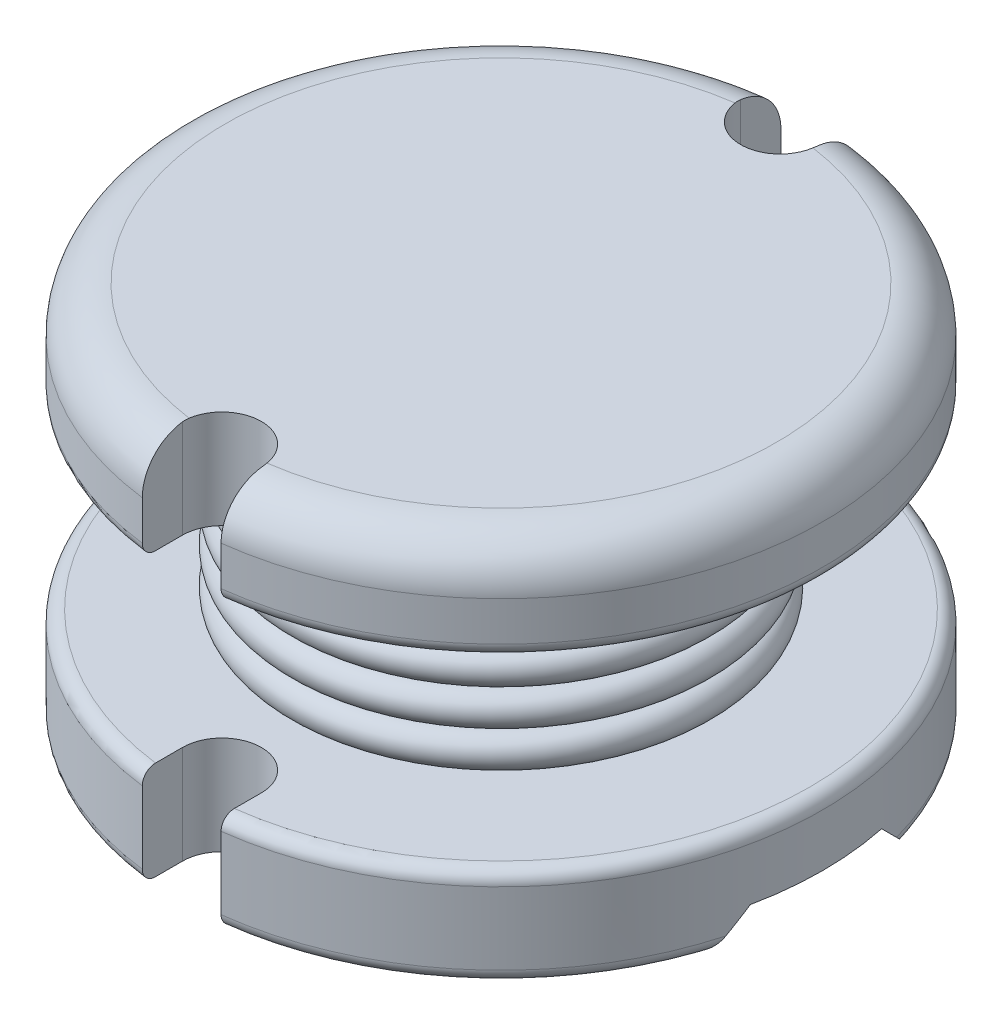
SolidWorks part; units mm, degrees
ref_plane "Front Plane" through (0, 0, 0) normal (0, 0, 1) x (1, 0, 0)
ref_plane "Top Plane" through (0, 0, 0) normal (0, 1, 0) x (1, 0, 0)
ref_plane "Right Plane" through (0, 0, 0) normal (1, 0, 0) x (0, 0, -1)
sketch "Sketch1" plane through (0, 0, 0) normal (0, 0, 1) x (1, 0, 0)
  line L0 (0, 0) -> (-4.7, 0)
  line L1 (-4.9, 0.2) -> (-4.9, 1.3)
  line L2 (-4.7, 1.5) -> (-2.6, 1.5)
  line L3 (-2.6, 1.5) -> (-2.6, 4.3)
  line L4 (-2.6, 4.3) -> (-4.7, 4.3)
  line L5 (-4.9, 4.5) -> (-4.9, 5.1)
  line L6 (-4.2, 5.8) -> (0, 5.8)
  line L7 (0, 5.8) -> (0, 0)
  arc A0 (-4.9, 5.1) -> (-4.2, 5.8) centre (-4.2, 5.1) cw
  arc A1 (-4.7, 0) -> (-4.9, 0.2) centre (-4.7, 0.2) cw
  arc A2 (-4.9, 1.3) -> (-4.7, 1.5) centre (-4.7, 1.3) cw
  arc A3 (-4.9, 4.5) -> (-4.7, 4.3) centre (-4.7, 4.5) ccw
  point P11 (-4.9, 5.8)
  point P14 (-4.9, 0)
  point P17 (-4.9, 1.5)
  point P20 (-4.9, 4.3)
  dimension "D6" = 0.7
  dimension "D7" = 0.2
  dimension "D1" = 5.8
  dimension "D2" = 4.9
  dimension "D3" = 1.5
  dimension "D4" = 1.5
  dimension "D5" = 2.6
revolve "Revolve1" add sketch "Sketch1" angle 360 about L7
sketch "Sketch2" plane through (0, 5.8, 0) normal (0, 1, 0) x (1, 0, 0)
  line L0 (0, 0) -> (0, 6) construction
  line L1 (0, 0) -> (0, -6) construction
  line L2 (-0.6, 6) -> (0.6, 6)
  line L3 (0.6, 6) -> (0.6, 4.25)
  line L4 (-0.6, 6) -> (-0.6, 4.25)
  line L5 (-0.6, -6) -> (0.6, -6)
  line L6 (0.6, -6) -> (0.6, -4.25)
  line L7 (-0.6, -6) -> (-0.6, -4.25)
  arc A0 (-0.6, -4.25) -> (0.6, -4.25) centre (0, -4.25) cw
  arc A1 (-0.6, 4.25) -> (0.6, 4.25) centre (0, 4.25) ccw
  dimension "D1" = 8.5
  dimension "D2" = 1.2
  dimension "D3" = 12
extrude "Cut-Extrude1" cut sketch "Sketch2" against normal through all
sketch "Sketch3" plane through (0, 0, 0) normal (0, 0, 1) x (1, 0, 0)
  line L0 (-0.6, 1.5) -> (-4.7, 1.5) construction
  line L1 (0, 0) -> (0, 6.5251) construction
  circle A0 centre (-3, 4) radius 0.25
  circle A1 centre (-3, 3.45) radius 0.25
  circle A2 centre (-3, 2.9) radius 0.25
  circle A3 centre (-3, 2.35) radius 0.25
  circle A4 centre (-3, 1.8) radius 0.25
  dimension "D1" = 0.5
  dimension "D4" = 0.55
  dimension "D5" = 0.55
  dimension "D7" = 3
  dimension "D2" = 0.55
  dimension "D3" = 0.55
  dimension "D6" = 0.3
revolve "Revolve2" add sketch "Sketch3" angle 360 about L1
sketch "Sketch4" plane through (0, 0, 0) normal (1, 0, 0) x (0, 0, -1)
  line L0 (-2, -0.5) -> (-1, 0.5)
  line L1 (-1, 0.5) -> (1, 0.5)
  line L2 (1, 0.5) -> (2, -0.5)
  line L3 (2, -0.5) -> (-2, -0.5)
  line L4 (0, -0.5) -> (0, 0) construction
  line L5 (-4.6615, 0) -> (4.6615, 0) construction
  dimension "D1" = 2
  dimension "D2" = 0.5
  dimension "D3" = 1
  dimension "D4" = 45
extrude "Cut-Extrude2" cut sketch "Sketch4" along normal through all and the other way blind 12
